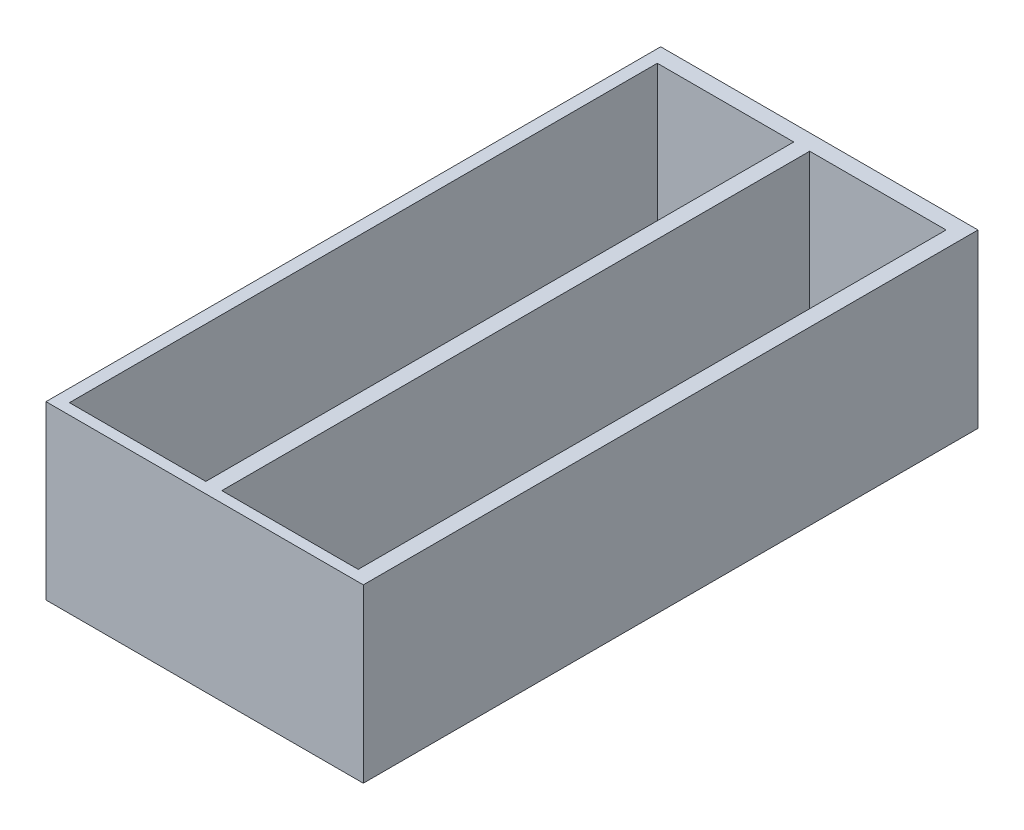
SolidWorks part; units mm, degrees
ref_plane "Front Plane" through (0, 0, 0) normal (0, 0, 1) x (1, 0, 0)
ref_plane "Top Plane" through (0, 0, 0) normal (0, 1, 0) x (1, 0, 0)
ref_plane "Right Plane" through (0, 0, 0) normal (1, 0, 0) x (0, 0, -1)
sketch "Sketch1" plane through (0, 0, 0) normal (0, 1, 0) x (1, 0, 0)
  line L1 (-27.2717, -18.3834) -> (12.5083, -18.3834)
  line L2 (-27.2717, -18.3834) -> (-27.2717, 58.6766)
  line L3 (-27.2717, 58.6766) -> (12.5083, 58.6766)
  line L4 (12.5083, -18.3834) -> (12.5083, 58.6766)
  dimension "D1" = 77.06
  dimension "D2" = 39.78
extrude "Boss-Extrude1" add sketch "Sketch1" along normal blind 21.54
sketch "Sketch2" plane through (0, 21.54, 0) normal (0, 1, 0) x (1, 0, 0)
  line L0 (12.5083, -18.3834) -> (12.5083, 58.6766) construction
  line L1 (10.5083, -17.0234) -> (-6.5917, -17.0234)
  line L2 (10.5083, -17.0234) -> (10.5083, 56.6766)
  line L3 (10.5083, 56.6766) -> (-6.5917, 56.6766)
  line L4 (-6.5917, -17.0234) -> (-6.5917, 56.6766)
  line L5 (12.5083, 58.6766) -> (-27.2717, 58.6766) construction
  line L6 (-8.5917, -17.0234) -> (-25.6917, -17.0234)
  line L7 (-8.5917, -17.0234) -> (-8.5917, 56.6766)
  line L8 (-8.5917, 56.6766) -> (-25.6917, 56.6766)
  line L9 (-25.6917, -17.0234) -> (-25.6917, 56.6766)
  dimension "D1" = 17.1
  dimension "D2" = 73.7
  dimension "D3" = 2
  dimension "D4" = 2
  dimension "D5" = 17.1
  dimension "D6" = 73.7
  dimension "D7" = 2
  dimension "D8" = 2
extrude "Cut-Extrude1" cut sketch "Sketch2" against normal blind 19.54
